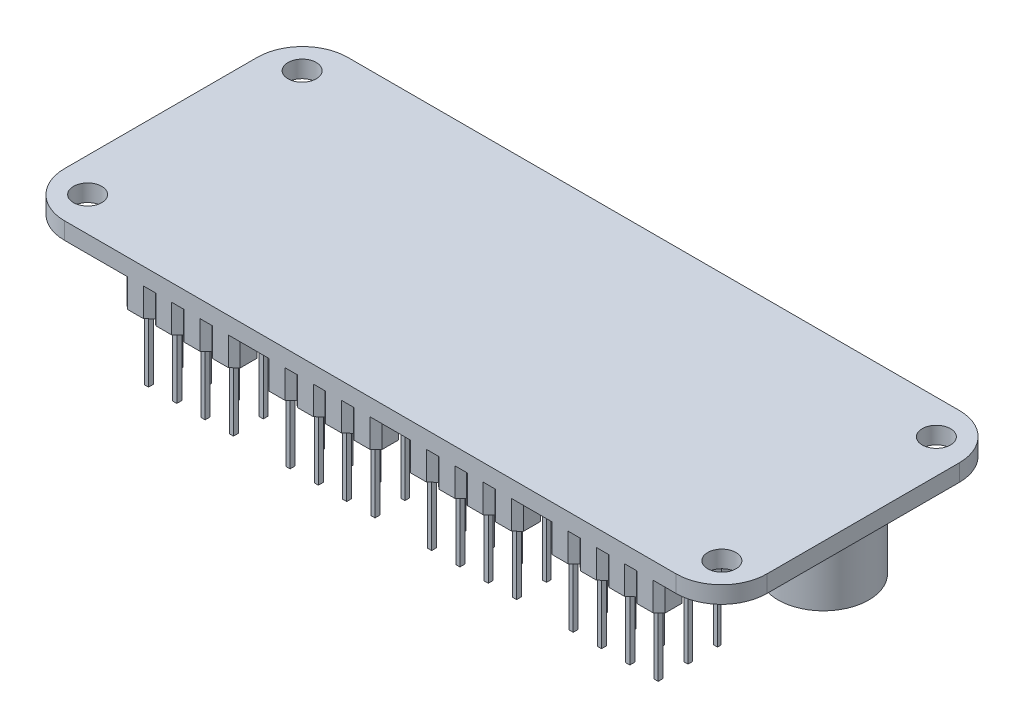
SolidWorks part; units mm, degrees
ref_plane "Alzado" through (0, 0, 0) normal (0, 0, 1) x (1, 0, 0)
ref_plane "Planta" through (0, 0, 0) normal (0, 1, 0) x (1, 0, 0)
ref_plane "Vista lateral" through (0, 0, 0) normal (1, 0, 0) x (0, 0, -1)
sketch "Croquis1" plane through (0, 0, 0) normal (0, 1, 0) x (1, 0, 0)
  line L1 (-31, 12.5) -> (31, 12.5)
  line L2 (-31, 12.5) -> (-31, -12.5)
  line L3 (-31, -12.5) -> (31, -12.5)
  line L4 (31, 12.5) -> (31, -12.5)
  line L5 (-31, 12.5) -> (31, -12.5) construction
  line L6 (-31, -12.5) -> (31, 12.5) construction
  point P0 (0, 0)
  dimension "D1" = 62
  dimension "D2" = 25
extrude "Saliente-Extruir1" add sketch "Croquis1" along normal blind 1.5
fillet "Redondeo1" radius 4 4 edges at (-31, 0.75, 12.5) (31, 0.75, 12.5) (31, 0.75, -12.5) (-31, 0.75, -12.5)
sketch "Croquis2" plane through (0, 1.5, 0) normal (0, 1, 0) x (1, 0, 0)
  line L1 (-28, 9.47) -> (28, 9.47) construction
  line L2 (-28, 9.47) -> (-28, -9.47) construction
  line L3 (-28, -9.47) -> (28, -9.47) construction
  line L4 (28, 9.47) -> (28, -9.47) construction
  line L5 (-28, 9.47) -> (28, -9.47) construction
  line L6 (-28, -9.47) -> (28, 9.47) construction
  circle A0 centre (-28, 9.47) radius 1.25
  circle A1 centre (28, 9.47) radius 1.25
  circle A2 centre (28, -9.47) radius 1.25
  circle A3 centre (-28, -9.47) radius 1.25
  point P0 (0, 0)
  dimension "D3" = 2.5
  dimension "D1" = 56
  dimension "D2" = 18.94
extrude "Cortar-Extruir1" cut sketch "Croquis2" against normal blind 10
sketch "Croquis3" plane through (0, 0, 0) normal (0, -1, 0) x (1, 0, 0)
  line L0 (31, 8.5) -> (31, -8.5) construction
  line L1 (27, -12.5) -> (-27, -12.5) construction
  circle A0 centre (19, -8.5) radius 4
  dimension "D1" = 8
  dimension "D3" = 4
  dimension "D2" = 12
extrude "Saliente-Extruir2" add sketch "Croquis3" along normal blind 13
sketch "Croquis4" plane through (0, 0, 0) normal (0, -1, 0) x (1, 0, 0)
  line L0 (-27, 12.5) -> (27, 12.5) construction
  line L1 (24.9512, 5) -> (23.5488, 5)
  line L2 (25.5, 5.5013) -> (25.5, 6.9987)
  line L3 (24.9512, 12.5) -> (23.5488, 12.5)
  line L4 (23, 5.5013) -> (23, 6.9987)
  line L5 (31, 8.5) -> (31, -8.5) construction
  line L8 (25.5, 6.9987) -> (24.9512, 7.5)
  line L9 (24.9512, 7.5) -> (25.5, 8.0013)
  line L10 (23, 6.9987) -> (23.5488, 7.5)
  line L11 (24.9512, 5) -> (25.5, 5.5013)
  line L12 (23.5488, 5) -> (23, 5.5013)
  line L13 (23.5488, 7.5) -> (23, 8.0013)
  line L14 (25.5, 9.4987) -> (24.9512, 10)
  line L15 (24.9512, 10) -> (25.5, 10.5013)
  line L16 (23.5488, 10) -> (23, 9.4987)
  line L17 (23.5488, 10) -> (23, 10.5013)
  line L18 (24.9512, 12.5) -> (25.5, 11.9987)
  line L19 (23.5488, 12.5) -> (23, 11.9987)
  line L20 (24.25, 5) -> (24.25, 12.5) construction
  line L21 (25.5, 8.75) -> (23, 8.75) construction
  line L22 (23.5488, 5) -> (23.5488, 12.5) construction
  line L23 (24.9512, 5) -> (24.9512, 12.5) construction
  line L24 (23, 8.0013) -> (23, 9.4987)
  line L25 (25.5, 8.0013) -> (25.5, 9.4987)
  line L26 (25.5, 10.5013) -> (25.5, 11.9987)
  line L27 (23, 10.5013) -> (23, 11.9987)
  dimension "D2" = 7.5
  dimension "D3" = 5.5
  dimension "D6" = 0.7433
extrude "Saliente-Extruir3" add sketch "Croquis4" along normal blind 2.5
sketch "Croquis5" plane through (0, -2.5, 0) normal (0, -1, 0) x (1, 0, 0)
  line L1 (24.4194, 5.9669) -> (24.0586, 5.9669)
  line L2 (24.4194, 5.9669) -> (24.4194, 6.2725)
  line L3 (24.4194, 6.2725) -> (24.0586, 6.2725)
  line L4 (24.0586, 5.9669) -> (24.0586, 6.2725)
  line L5 (24.4194, 8.4711) -> (24.0586, 8.4711)
  line L6 (24.4194, 8.4711) -> (24.4194, 8.8781)
  line L7 (24.4194, 8.8781) -> (24.0586, 8.8781)
  line L8 (24.0586, 8.4711) -> (24.0586, 8.8781)
  line L9 (24.4194, 11.0767) -> (24.0586, 11.0767)
  line L10 (24.4194, 11.0767) -> (24.4194, 11.5156)
  line L11 (24.4194, 11.5156) -> (24.0586, 11.5156)
  line L12 (24.0586, 11.0767) -> (24.0586, 11.5156)
extrude "Saliente-Extruir4" add sketch "Croquis5" along normal blind 6
pattern_linear "MatrizL1" count 4 spacing 2.5 along (-1, 0, 0) of "Saliente-Extruir3", "Saliente-Extruir4"
pattern_linear "MatrizL2" count 4 spacing 12.5 along (-1, 0, 0) of "MatrizL1", "Saliente-Extruir3", "Saliente-Extruir4"
